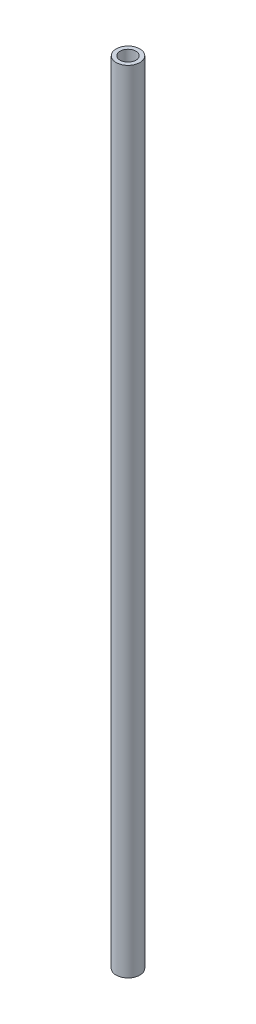
SolidWorks part; units mm, degrees
ref_plane "정면" through (0, 0, 0) normal (0, 0, 1) x (1, 0, 0)
ref_plane "윗면" through (0, 0, 0) normal (0, 1, 0) x (1, 0, 0)
ref_plane "우측면" through (0, 0, 0) normal (1, 0, 0) x (0, 0, -1)
sketch "스케치1" plane through (0, 0, 0) normal (0, 1, 0) x (1, 0, 0)
  circle A0 centre (0, 0) radius 3
  circle A1 centre (0, 0) radius 2
  dimension "D1" = 6
  dimension "D2" = 4
extrude "보스-돌출1" add sketch "스케치1" along normal blind 200
sketch "스케치2" plane through (0, 0, 0) normal (0, -1, 0) x (1, 0, 0)
  circle A0 centre (0, 0) radius 2
extrude "보스-돌출2" add sketch "스케치2" against normal blind 3 from offset 10 offset against normal yes
sketch "스케치3" plane through (0, 200, 0) normal (0, 1, 0) x (1, 0, 0)
  circle A0 centre (0, 0) radius 2
extrude "보스-돌출3" add sketch "스케치3" against normal blind 3 from offset 10
